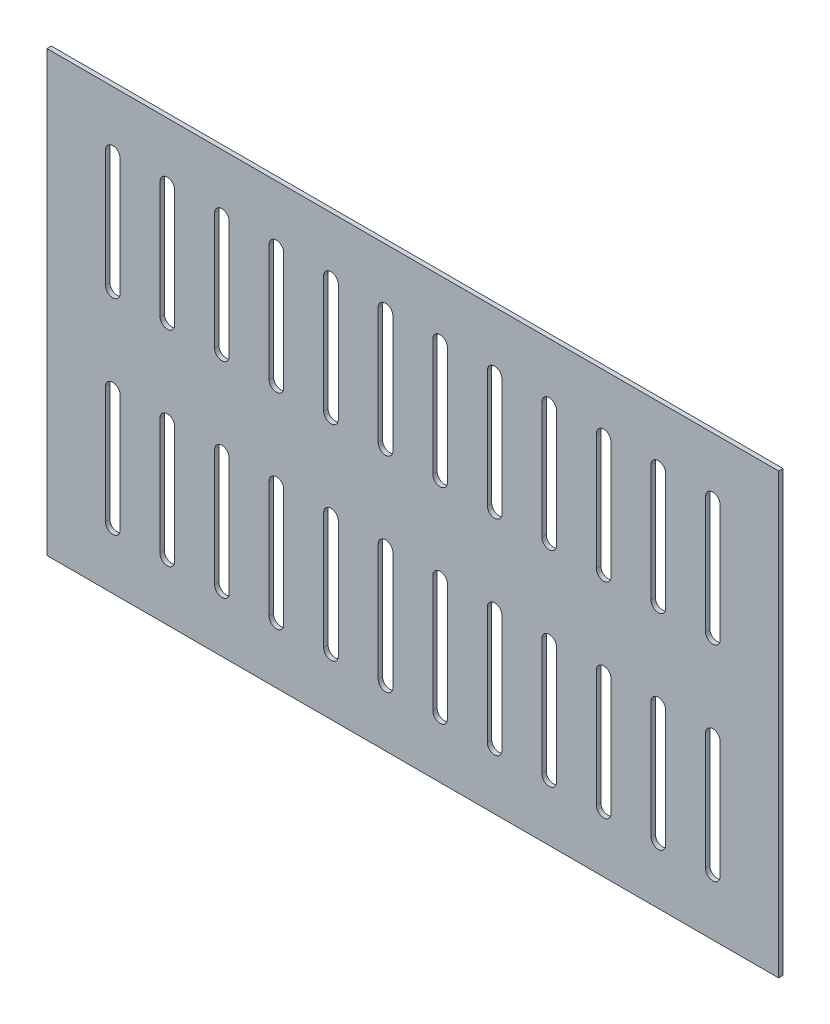
SolidWorks part; units mm, degrees
ref_plane "Ön Düzlem" through (0, 0, 0) normal (0, 0, 1) x (1, 0, 0)
ref_plane "Üst Düzlem" through (0, 0, 0) normal (0, 1, 0) x (1, 0, 0)
ref_plane "Sağ Düzlem" through (0, 0, 0) normal (1, 0, 0) x (0, 0, -1)
sketch "Çizim1" plane through (0, 0, 0) normal (0, 0, 1) x (1, 0, 0)
  line L0 (45, -40) -> (45, -120) construction
  line L1 (0, 0) -> (500, 0)
  line L2 (0, 0) -> (0, -300)
  line L3 (0, -300) -> (500, -300)
  line L4 (500, 0) -> (500, -300)
  line L5 (50, -40) -> (50, -120)
  line L6 (40, -40) -> (40, -120)
  line L7 (82.2727, -40) -> (82.2727, -120) construction
  line L8 (87.2727, -40) -> (87.2727, -120)
  line L9 (77.2727, -40) -> (77.2727, -120)
  line L10 (119.5455, -40) -> (119.5455, -120) construction
  line L11 (124.5455, -40) -> (124.5455, -120)
  line L12 (114.5455, -40) -> (114.5455, -120)
  line L13 (156.8182, -40) -> (156.8182, -120) construction
  line L14 (161.8182, -40) -> (161.8182, -120)
  line L15 (151.8182, -40) -> (151.8182, -120)
  line L16 (194.0909, -40) -> (194.0909, -120) construction
  line L17 (199.0909, -40) -> (199.0909, -120)
  line L18 (189.0909, -40) -> (189.0909, -120)
  line L19 (231.3636, -40) -> (231.3636, -120) construction
  line L20 (236.3636, -40) -> (236.3636, -120)
  line L21 (226.3636, -40) -> (226.3636, -120)
  line L22 (268.6364, -40) -> (268.6364, -120) construction
  line L23 (273.6364, -40) -> (273.6364, -120)
  line L24 (263.6364, -40) -> (263.6364, -120)
  line L25 (305.9091, -40) -> (305.9091, -120) construction
  line L26 (310.9091, -40) -> (310.9091, -120)
  line L27 (300.9091, -40) -> (300.9091, -120)
  line L28 (343.1818, -40) -> (343.1818, -120) construction
  line L29 (348.1818, -40) -> (348.1818, -120)
  line L30 (338.1818, -40) -> (338.1818, -120)
  line L31 (380.4545, -40) -> (380.4545, -120) construction
  line L32 (385.4545, -40) -> (385.4545, -120)
  line L33 (375.4545, -40) -> (375.4545, -120)
  line L34 (417.7273, -40) -> (417.7273, -120) construction
  line L35 (422.7273, -40) -> (422.7273, -120)
  line L36 (412.7273, -40) -> (412.7273, -120)
  line L37 (455, -40) -> (455, -120) construction
  line L38 (460, -40) -> (460, -120)
  line L39 (450, -40) -> (450, -120)
  line L40 (82.2727, -180) -> (82.2727, -260) construction
  line L41 (87.2727, -180) -> (87.2727, -260)
  line L42 (77.2727, -180) -> (77.2727, -260)
  line L43 (119.5455, -180) -> (119.5455, -260) construction
  line L44 (124.5455, -180) -> (124.5455, -260)
  line L45 (114.5455, -180) -> (114.5455, -260)
  line L46 (156.8182, -180) -> (156.8182, -260) construction
  line L47 (161.8182, -180) -> (161.8182, -260)
  line L48 (151.8182, -180) -> (151.8182, -260)
  line L49 (194.0909, -180) -> (194.0909, -260) construction
  line L50 (199.0909, -180) -> (199.0909, -260)
  line L51 (189.0909, -180) -> (189.0909, -260)
  line L52 (231.3636, -180) -> (231.3636, -260) construction
  line L53 (236.3636, -180) -> (236.3636, -260)
  line L54 (226.3636, -180) -> (226.3636, -260)
  line L55 (268.6364, -180) -> (268.6364, -260) construction
  line L56 (273.6364, -180) -> (273.6364, -260)
  line L57 (263.6364, -180) -> (263.6364, -260)
  line L58 (305.9091, -180) -> (305.9091, -260) construction
  line L59 (310.9091, -180) -> (310.9091, -260)
  line L60 (300.9091, -180) -> (300.9091, -260)
  line L61 (343.1818, -180) -> (343.1818, -260) construction
  line L62 (348.1818, -180) -> (348.1818, -260)
  line L63 (338.1818, -180) -> (338.1818, -260)
  line L64 (380.4545, -180) -> (380.4545, -260) construction
  line L65 (385.4545, -180) -> (385.4545, -260)
  line L66 (375.4545, -180) -> (375.4545, -260)
  line L67 (417.7273, -180) -> (417.7273, -260) construction
  line L68 (422.7273, -180) -> (422.7273, -260)
  line L69 (412.7273, -180) -> (412.7273, -260)
  line L70 (455, -180) -> (455, -260) construction
  line L71 (460, -180) -> (460, -260)
  line L72 (450, -180) -> (450, -260)
  line L73 (45, -180) -> (45, -260) construction
  line L74 (50, -180) -> (50, -260)
  line L75 (40, -180) -> (40, -260)
  arc A0 (50, -40) -> (40, -40) centre (45, -40) ccw
  arc A1 (40, -120) -> (50, -120) centre (45, -120) ccw
  arc A2 (87.2727, -40) -> (77.2727, -40) centre (82.2727, -40) ccw
  arc A3 (77.2727, -120) -> (87.2727, -120) centre (82.2727, -120) ccw
  arc A4 (124.5455, -40) -> (114.5455, -40) centre (119.5455, -40) ccw
  arc A5 (114.5455, -120) -> (124.5455, -120) centre (119.5455, -120) ccw
  arc A6 (161.8182, -40) -> (151.8182, -40) centre (156.8182, -40) ccw
  arc A7 (151.8182, -120) -> (161.8182, -120) centre (156.8182, -120) ccw
  arc A8 (199.0909, -40) -> (189.0909, -40) centre (194.0909, -40) ccw
  arc A9 (189.0909, -120) -> (199.0909, -120) centre (194.0909, -120) ccw
  arc A10 (236.3636, -40) -> (226.3636, -40) centre (231.3636, -40) ccw
  arc A11 (226.3636, -120) -> (236.3636, -120) centre (231.3636, -120) ccw
  arc A12 (273.6364, -40) -> (263.6364, -40) centre (268.6364, -40) ccw
  arc A13 (263.6364, -120) -> (273.6364, -120) centre (268.6364, -120) ccw
  arc A14 (310.9091, -40) -> (300.9091, -40) centre (305.9091, -40) ccw
  arc A15 (300.9091, -120) -> (310.9091, -120) centre (305.9091, -120) ccw
  arc A16 (348.1818, -40) -> (338.1818, -40) centre (343.1818, -40) ccw
  arc A17 (338.1818, -120) -> (348.1818, -120) centre (343.1818, -120) ccw
  arc A18 (385.4545, -40) -> (375.4545, -40) centre (380.4545, -40) ccw
  arc A19 (375.4545, -120) -> (385.4545, -120) centre (380.4545, -120) ccw
  arc A20 (422.7273, -40) -> (412.7273, -40) centre (417.7273, -40) ccw
  arc A21 (412.7273, -120) -> (422.7273, -120) centre (417.7273, -120) ccw
  arc A22 (460, -40) -> (450, -40) centre (455, -40) ccw
  arc A23 (450, -120) -> (460, -120) centre (455, -120) ccw
  arc A24 (87.2727, -180) -> (77.2727, -180) centre (82.2727, -180) ccw
  arc A25 (77.2727, -260) -> (87.2727, -260) centre (82.2727, -260) ccw
  arc A26 (124.5455, -180) -> (114.5455, -180) centre (119.5455, -180) ccw
  arc A27 (114.5455, -260) -> (124.5455, -260) centre (119.5455, -260) ccw
  arc A28 (161.8182, -180) -> (151.8182, -180) centre (156.8182, -180) ccw
  arc A29 (151.8182, -260) -> (161.8182, -260) centre (156.8182, -260) ccw
  arc A30 (199.0909, -180) -> (189.0909, -180) centre (194.0909, -180) ccw
  arc A31 (189.0909, -260) -> (199.0909, -260) centre (194.0909, -260) ccw
  arc A32 (236.3636, -180) -> (226.3636, -180) centre (231.3636, -180) ccw
  arc A33 (226.3636, -260) -> (236.3636, -260) centre (231.3636, -260) ccw
  arc A34 (273.6364, -180) -> (263.6364, -180) centre (268.6364, -180) ccw
  arc A35 (263.6364, -260) -> (273.6364, -260) centre (268.6364, -260) ccw
  arc A36 (310.9091, -180) -> (300.9091, -180) centre (305.9091, -180) ccw
  arc A37 (300.9091, -260) -> (310.9091, -260) centre (305.9091, -260) ccw
  arc A38 (348.1818, -180) -> (338.1818, -180) centre (343.1818, -180) ccw
  arc A39 (338.1818, -260) -> (348.1818, -260) centre (343.1818, -260) ccw
  arc A40 (385.4545, -180) -> (375.4545, -180) centre (380.4545, -180) ccw
  arc A41 (375.4545, -260) -> (385.4545, -260) centre (380.4545, -260) ccw
  arc A42 (422.7273, -180) -> (412.7273, -180) centre (417.7273, -180) ccw
  arc A43 (412.7273, -260) -> (422.7273, -260) centre (417.7273, -260) ccw
  arc A44 (460, -180) -> (450, -180) centre (455, -180) ccw
  arc A45 (450, -260) -> (460, -260) centre (455, -260) ccw
  arc A46 (50, -180) -> (40, -180) centre (45, -180) ccw
  arc A47 (40, -260) -> (50, -260) centre (45, -260) ccw
  point P7 (45, -80)
  point P16 (82.2727, -80)
  point P23 (119.5455, -80)
  point P30 (156.8182, -80)
  point P37 (194.0909, -80)
  point P44 (231.3636, -80)
  point P51 (268.6364, -80)
  point P58 (305.9091, -80)
  point P65 (343.1818, -80)
  point P72 (380.4545, -80)
  point P79 (417.7273, -80)
  point P86 (455, -80)
  point P93 (82.2727, -220)
  point P100 (119.5455, -220)
  point P107 (156.8182, -220)
  point P114 (194.0909, -220)
  point P121 (231.3636, -220)
  point P128 (268.6364, -220)
  point P135 (305.9091, -220)
  point P142 (343.1818, -220)
  point P149 (380.4545, -220)
  point P156 (417.7273, -220)
  point P163 (455, -220)
  point P170 (45, -220)
  dimension "D5" = 40
  dimension "D11" = 60
  dimension "D1" = 500
  dimension "D2" = 300
  dimension "D3" = 10
  dimension "D4" = 80
  dimension "D6" = 40
  dimension "D9" = 40
  dimension "D10" = 40
  dimension "D7" = 12
  dimension "D8" = 2
extrude "Yükseklik-Ekstrüzyon1" add sketch "Çizim1" along normal blind 3
